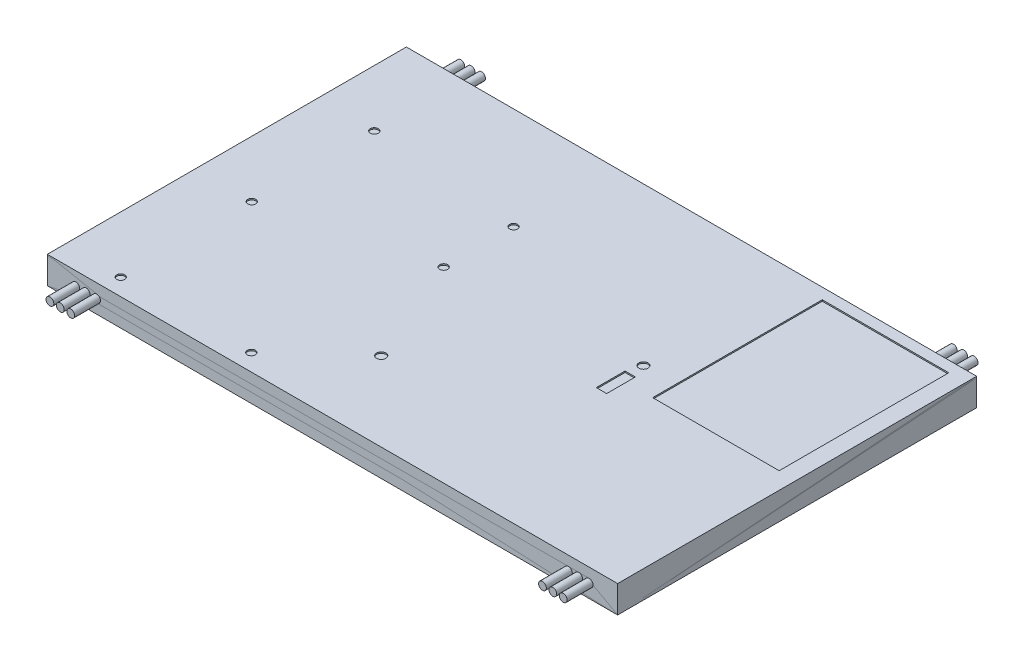
SolidWorks part; units mm, degrees
ref_plane "Front Plane" through (0, 0, 0) normal (0, 0, 1) x (1, 0, 0)
ref_plane "Top Plane" through (0, 0, 0) normal (0, 1, 0) x (1, 0, 0)
ref_plane "Right Plane" through (0, 0, 0) normal (1, 0, 0) x (0, 0, -1)
sketch "Sketch1" plane through (0, 0, 0) normal (0, 1, 0) x (1, 0, 0)
  line L0 (-106.9643, -60.8334) -> (113.0357, -60.8334)
  line L1 (113.0357, -60.8334) -> (113.0357, 77.6666)
  line L2 (113.0357, 77.6666) -> (-106.9643, 77.6666)
  line L3 (-106.9643, 77.6666) -> (-106.9643, -60.8334)
extrude "Boss-Extrude1" add sketch "Sketch1" along normal blind 10 contours L3 L0 L1 L2
sketch "Sketch2" plane through (0, 10, 0) normal (0, 1, 0) x (1, 0, 0)
  line L0 (3.0357, -60.8334) -> (3.0357, 77.6666)
  line L1 (-106.9643, -60.8334) -> (113.0357, -60.8334) construction
  line L7 (113.0357, 77.6666) -> (-106.9643, 77.6666) construction
  line L15 (113.0357, 8.4166) -> (-106.9643, 8.4166)
  line L16 (113.0357, -60.8334) -> (113.0357, 77.6666) construction
  line L17 (-106.9643, 77.6666) -> (-106.9643, -60.8334) construction
sketch "Sketch5" plane through (0, 0, 0) normal (0, 1, 0) x (1, 0, 0)
  line L0 (-106.9643, 8.4166) -> (-106.9643, 77.6666)
  line L1 (-106.9643, 77.6666) -> (113.0357, 77.6666)
  line L2 (113.0357, 77.6666) -> (113.0357, -60.8334)
  line L3 (113.0357, -60.8334) -> (-106.9643, -60.8334)
  line L4 (-106.9643, -60.8334) -> (-106.9643, 8.4166)
extrude "Boss-Extrude3" add sketch "Sketch5" along normal blind 10.51 separate body contours L4 L0 L1 L2 L3
ref_plane "Plane3" through (0, 0, 70.8334) normal (0, 0, 1) x (1, 0, 0)
sketch "Sketch6" plane through (0, 0, 70.8334) normal (0, 0, 1) x (1, 0, 0)
  line L0 (-106.9643, 5.255) -> (-95.9643, 5.255)
  line L1 (-106.9643, 10.51) -> (-106.9643, 0) construction
  line L2 (-95.9643, 5.255) -> (-91.9543, 5.255)
  line L3 (-91.9543, 5.255) -> (-87.9443, 5.255)
  line L4 (-87.9443, 5.255) -> (94.0457, 5.255)
  line L5 (94.0457, 5.255) -> (98.0457, 5.255)
  line L6 (98.0457, 5.255) -> (102.0457, 5.255)
  circle A0 centre (-95.9643, 5.255) radius 1.505
  circle A1 centre (-91.9543, 5.255) radius 1.505
  circle A2 centre (-87.9443, 5.255) radius 1.505
  circle A3 centre (94.0457, 5.255) radius 1.505
  circle A4 centre (98.0457, 5.255) radius 1.505
  circle A5 centre (102.0457, 5.255) radius 1.505
extrude "Boss-Extrude4" add sketch "Sketch6" against normal blind 16.5 contours A0 | A1 | A2 | A5 | A4 | A3
sketch "Sketch7" plane through (0, 0, 0) normal (0, 1, 0) x (1, 0, 0)
  line L1 (57.6862, 73.452) -> (106.4952, 73.452)
  line L2 (57.6862, 73.452) -> (57.6862, 8.0272)
  line L3 (57.6862, 8.0272) -> (106.4952, 8.0272)
  line L4 (106.4952, 73.452) -> (106.4952, 8.0272)
  line L5 (57.6862, 73.452) -> (106.4952, 8.0272) construction
  line L6 (57.6862, 8.0272) -> (106.4952, 73.452) construction
  point P0 (82.0907, 40.7396)
extrude "Cut-Extrude1" cut sketch "Sketch7" along normal blind 75 and the other way blind 81
ref_plane "Plane4" through (0, 0, -87.6666) normal (0, 0, -1) x (-1, 0, 0)
sketch "Sketch8" plane through (0, 0, -87.6666) normal (0, 0, -1) x (-1, 0, 0)
  line L0 (106.9643, 5.255) -> (95.9643, 5.255)
  line L1 (106.9643, 10.51) -> (106.9643, 0) construction
  line L2 (95.9643, 5.255) -> (91.9543, 5.255)
  line L3 (91.9543, 5.255) -> (87.9443, 5.255)
  line L4 (87.9443, 5.255) -> (-94.0457, 5.255)
  line L5 (-94.0457, 5.255) -> (-98.0457, 5.255)
  line L6 (-98.0457, 5.255) -> (-102.0457, 5.255)
  circle A0 centre (-102.0457, 5.255) radius 1.505
  circle A1 centre (-98.0457, 5.255) radius 1.55
  circle A2 centre (-94.0457, 5.255) radius 1.505
  circle A3 centre (95.9643, 5.255) radius 1.505
  circle A4 centre (91.9543, 5.255) radius 1.505
  circle A5 centre (87.9443, 5.255) radius 1.505
extrude "Boss-Extrude5" add sketch "Sketch8" against normal blind 12 contours A0 | A1 | A2 | A5 | A4 | A3
sketch "Sketch9" plane through (0, 0, 0) normal (0, 1, 0) x (1, 0, 0)
  line L12 (43.4556, 0.5196) -> (47.452, 0.5196)
  line L13 (47.452, 0.5196) -> (47.4556, 11.6052)
  line L14 (47.4556, 11.6052) -> (43.4556, 11.6052)
  line L15 (43.4556, 11.6052) -> (43.4556, 0.5196)
  circle A0 centre (-85.1613, -54.2946) radius 1.55
  circle A2 centre (-34.7813, -54.2946) radius 1.55
  circle A6 centre (-85.1061, -3.8254) radius 1.55
  circle A8 centre (-26.2561, 11.3746) radius 1.55
  circle A11 centre (-26.2561, 38.3346) radius 1.55
  circle A12 centre (-85.1061, 43.4346) radius 1.55
  circle A15 centre (45.1801, 16.9956) radius 1.7759
  circle A16 centre (-8.6887, -30.2987) radius 1.7996
  point P17 (43.4556, 0.5196)
  dimension "D1" = 50.38
  dimension "D3" = 3.1
  dimension "D9" = 3.1
  dimension "D5" = 58.85
  dimension "D6" = 58.85
extrude "Cut-Extrude2" cut sketch "Sketch9" against normal blind 51 and the other way blind 65
